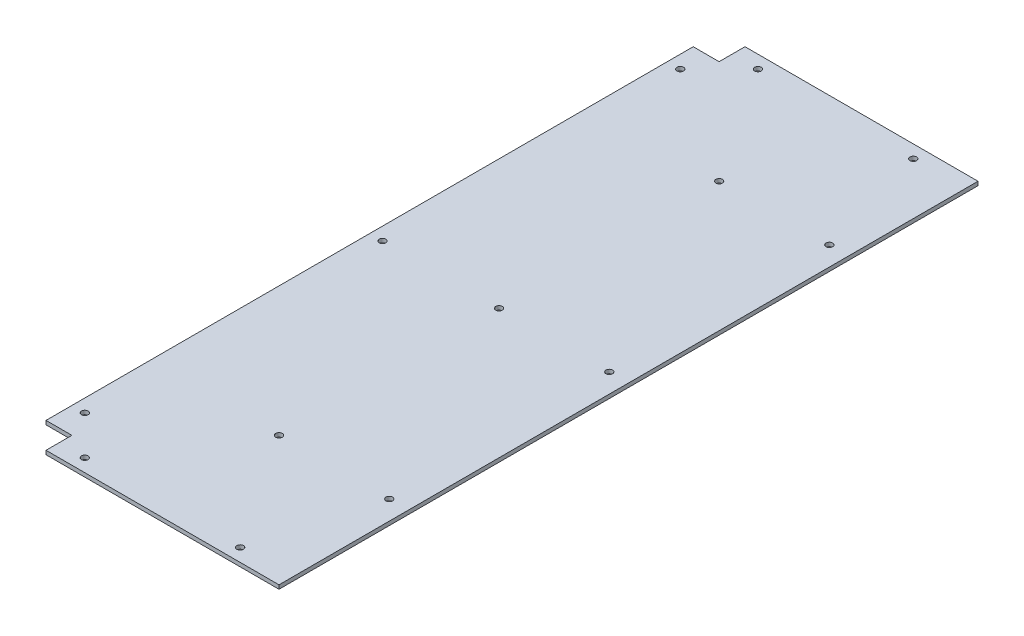
SolidWorks part; units mm, degrees
ref_plane "Front Plane" through (0, 0, 0) normal (0, 0, 1) x (1, 0, 0)
ref_plane "Top Plane" through (0, 0, 0) normal (0, 1, 0) x (1, 0, 0)
ref_plane "Right Plane" through (0, 0, 0) normal (1, 0, 0) x (0, 0, -1)
sketch "Sketch1" plane through (0, 0, 0) normal (0, 1, 0) x (1, 0, 0)
  line L0 (-80, 270) -> (-80, 250)
  line L1 (-80, 270) -> (100, 270)
  line L2 (-100, 250) -> (-100, -250)
  line L3 (-80, -270) -> (100, -270)
  line L4 (100, 270) -> (100, -270)
  line L5 (-100, 270) -> (100, -270) construction
  line L6 (-100, -270) -> (100, 270) construction
  line L7 (-80, 250) -> (-100, 250)
  line L8 (-100, -250) -> (-80, -250)
  line L9 (-80, -250) -> (-80, -270)
  circle A0 centre (-60, 260) radius 2.55
  circle A1 centre (60, 260) radius 2.55
  circle A2 centre (-90, 230) radius 2.55
  circle A3 centre (-90, 0) radius 2.55
  circle A4 centre (-90, -230) radius 2.55
  circle A5 centre (60, -260) radius 2.55
  circle A6 centre (0, 0) radius 2.55
  circle A7 centre (0, 170) radius 2.55
  circle A8 centre (0, -170) radius 2.55
  circle A9 centre (-60, -260) radius 2.55
  circle A10 centre (85.1649, 0) radius 2.55
  circle A11 centre (85.1649, 170) radius 2.55
  circle A12 centre (85.1649, -170) radius 2.55
  point P0 (0, 0)
  dimension "D3" = 10
  dimension "D4" = 10
  dimension "D5" = 40
  dimension "D6" = 40
  dimension "D7" = 10
  dimension "D8" = 40
  dimension "D9" = 10
  dimension "D10" = 10
  dimension "D11" = 40
  dimension "D12" = 10
  dimension "D13" = 40
  dimension "D14" = 10
  dimension "D15" = 40
  dimension "D17" = 100
  dimension "D18" = 5.1
  dimension "D24" = 5.1
  dimension "D16" = 100
  dimension "D19" = 20
  dimension "D20" = 20
  dimension "D21" = 20
  dimension "D22" = 200
  dimension "D23" = 540
extrude "Boss-Extrude1" add sketch "Sketch1" along normal blind 3
